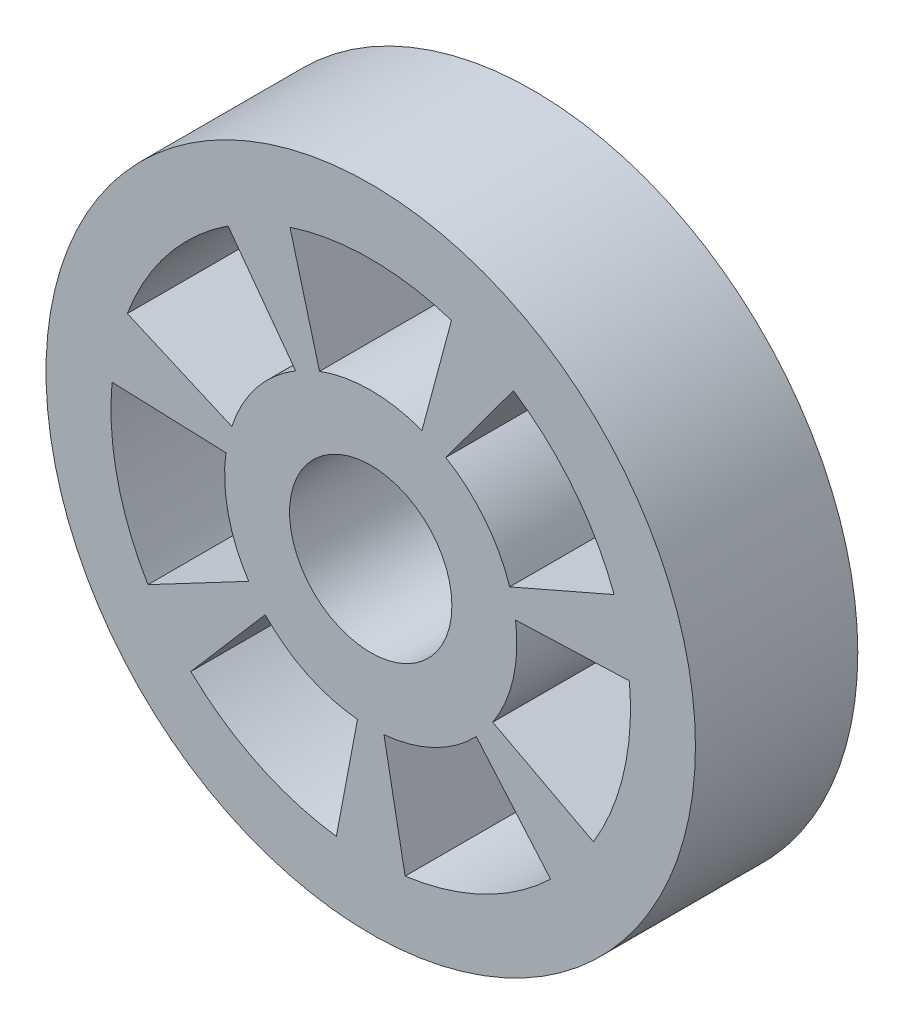
SolidWorks part; units mm, degrees
material "ABS"
ref_plane "Front Plane" through (0, 0, 0) normal (0, 0, 1) x (1, 0, 0)
ref_plane "Top Plane" through (0, 0, 0) normal (0, 1, 0) x (1, 0, 0)
ref_plane "Right Plane" through (0, 0, 0) normal (1, 0, 0) x (0, 0, -1)
sketch "Sketch1" plane through (0, 0, 0) normal (0, 0, 1) x (1, 0, 0)
  line L0 (7.8897, 21.0714) -> (12.4309, 38.0194)
  line L1 (-7.8897, 21.0714) -> (-12.4309, 38.0194)
  line L2 (0, 0) -> (0, 86.1275) construction
  line L3 (21.3934, 6.9693) -> (37.4753, 13.9858)
  line L4 (11.5551, 19.3062) -> (21.9742, 33.4236)
  line L5 (18.7874, -12.3807) -> (34.3, -20.5794)
  line L6 (22.2987, 3.0031) -> (39.8323, 3.6592)
  line L7 (2.0341, -22.4079) -> (5.2961, -39.6478)
  line L8 (16.2509, -15.5614) -> (27.6959, -28.8607)
  line L9 (-16.2509, -15.5614) -> (-27.6959, -28.8607)
  line L10 (-2.0341, -22.4079) -> (-5.2961, -39.6478)
  line L11 (-22.2987, 3.0031) -> (-39.8323, 3.6592)
  line L12 (-18.7874, -12.3807) -> (-34.3, -20.5794)
  line L13 (-11.5551, 19.3062) -> (-21.9742, 33.4236)
  line L14 (-21.3934, 6.9693) -> (-37.4753, 13.9858)
  circle A0 centre (0, 0) radius 50
  circle A1 centre (0, 0) radius 12.5
  arc A2 (7.8897, 21.0714) -> (-7.8897, 21.0714) centre (0, 0) ccw
  circle A3 centre (0, 0) radius 40 construction
  circle A4 centre (0, 0) radius 22.5 construction
  arc A5 (-12.4309, 38.0194) -> (12.4309, 38.0194) centre (0, 0) cw
  arc A6 (21.9742, 33.4236) -> (37.4753, 13.9858) centre (0, 0) cw
  arc A7 (21.3934, 6.9693) -> (11.5551, 19.3062) centre (0, 0) ccw
  arc A8 (39.8323, 3.6592) -> (34.3, -20.5794) centre (0, 0) cw
  arc A9 (18.7874, -12.3807) -> (22.2987, 3.0031) centre (0, 0) ccw
  arc A10 (27.6959, -28.8607) -> (5.2961, -39.6478) centre (0, 0) cw
  arc A11 (2.0341, -22.4079) -> (16.2509, -15.5614) centre (0, 0) ccw
  arc A12 (-5.2961, -39.6478) -> (-27.6959, -28.8607) centre (0, 0) cw
  arc A13 (-16.2509, -15.5614) -> (-2.0341, -22.4079) centre (0, 0) ccw
  arc A14 (-34.3, -20.5794) -> (-39.8323, 3.6592) centre (0, 0) cw
  arc A15 (-22.2987, 3.0031) -> (-18.7874, -12.3807) centre (0, 0) ccw
  arc A16 (-37.4753, 13.9858) -> (-21.9742, 33.4236) centre (0, 0) cw
  arc A17 (-11.5551, 19.3062) -> (-21.3934, 6.9693) centre (0, 0) ccw
  point P40 (0, 0)
  dimension "D1" = 100
  dimension "D2" = 25
  dimension "D5" = 30
  dimension "D6" = 15
  dimension "D7" = 7
  dimension "D3" = 10
  dimension "D4" = 10
extrude "Boss-Extrude1" add sketch "Sketch1" along normal blind 25
